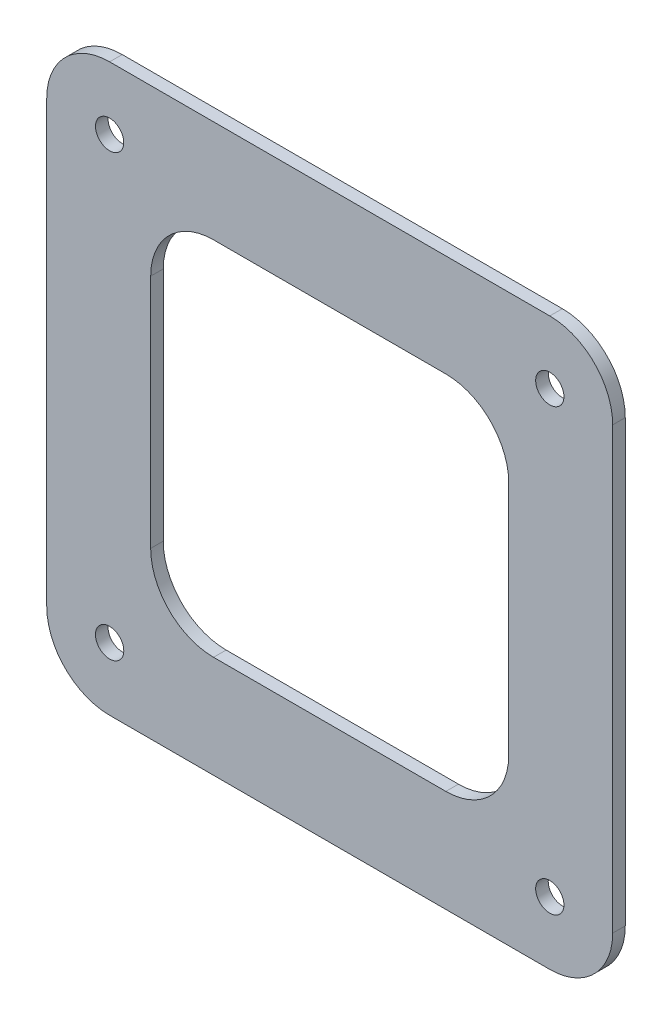
SolidWorks part; units mm, degrees
ref_plane "Plan de face" through (0, 0, 0) normal (0, 0, 1) x (1, 0, 0)
ref_plane "Plan de dessus" through (0, 0, 0) normal (0, 1, 0) x (1, 0, 0)
ref_plane "Plan de droite" through (0, 0, 0) normal (1, 0, 0) x (0, 0, -1)
sketch "Esquisse1" plane through (0, 0, 0) normal (0, 0, 1) x (1, 0, 0)
  line L1 (35, -45) -> (-35, -45)
  line L2 (45, -35) -> (45, 35)
  line L3 (35, 45) -> (-35, 45)
  line L4 (-45, -35) -> (-45, 35)
  line L5 (45, -45) -> (-45, 45) construction
  line L6 (45, 45) -> (-45, -45) construction
  arc A0 (45, 35) -> (35, 45) centre (35, 35) ccw
  arc A1 (-35, 45) -> (-45, 35) centre (-35, 35) ccw
  arc A2 (-35, -45) -> (-45, -35) centre (-35, -35) cw
  arc A3 (45, -35) -> (35, -45) centre (35, -35) cw
  point P0 (0, 0)
  dimension "D3" = 10
  dimension "D4" = 10
  dimension "D1" = 90
  dimension "D2" = 90
extrude "Boss.-Extru.1" add sketch "Esquisse1" along normal blind 2
sketch "Esquisse2" plane through (0, 0, 0) normal (0, 0, -1) x (-1, 0, 0)
  line L0 (0, 0) -> (-50000, 0) construction
  line L1 (0, 0) -> (0, 50000) construction
  circle A0 centre (-35, -35) radius 2.25
  arc A1 (-45, -35) -> (-35, -45) centre (-35, -35) ccw construction
  circle A2 centre (-35, 35) radius 2.25
  circle A3 centre (35, -35) radius 2.25
  circle A4 centre (35, 35) radius 2.25
  dimension "D1" = 4.5
extrude "Enlèv. mat.-Extru.1" cut sketch "Esquisse2" against normal through all
sketch "Esquisse4" plane through (0, 0, 0) normal (0, 0, -1) x (-1, 0, 0)
  line L1 (-18.4715, -28.7452) -> (18.4715, -28.7452)
  line L2 (-28.4715, -18.7452) -> (-28.4715, 18.7452)
  line L3 (-18.4715, 28.7452) -> (18.4715, 28.7452)
  line L4 (28.4715, -18.7452) -> (28.4715, 18.7452)
  line L5 (-28.4715, -28.7452) -> (28.4715, 28.7452) construction
  line L6 (-28.4715, 28.7452) -> (28.4715, -28.7452) construction
  arc A0 (18.4715, 28.7452) -> (28.4715, 18.7452) centre (18.4715, 18.7452) cw
  arc A1 (18.4715, -28.7452) -> (28.4715, -18.7452) centre (18.4715, -18.7452) ccw
  arc A2 (-18.4715, -28.7452) -> (-28.4715, -18.7452) centre (-18.4715, -18.7452) cw
  arc A3 (-28.4715, 18.7452) -> (-18.4715, 28.7452) centre (-18.4715, 18.7452) cw
  point P0 (0, 0)
  dimension "D1" = 10
extrude "Enlèv. mat.-Extru.2" cut sketch "Esquisse4" against normal blind 10
